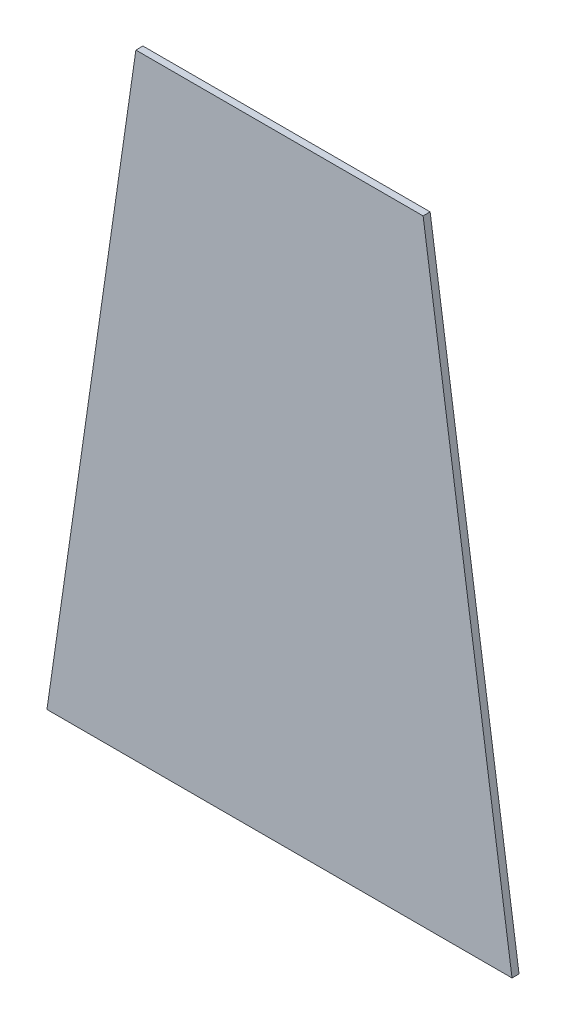
SolidWorks part; units mm, degrees
ref_plane "Front Plane" through (0, 0, 0) normal (0, 0, 1) x (1, 0, 0)
ref_plane "Top Plane" through (0, 0, 0) normal (0, 1, 0) x (1, 0, 0)
ref_plane "Right Plane" through (0, 0, 0) normal (1, 0, 0) x (0, 0, -1)
sketch "Sketch1" plane through (0, 0, 0) normal (0, 0, 1) x (1, 0, 0)
  line L0 (-66.675, 142.875) -> (-107.95, -142.875)
  line L1 (66.675, 142.875) -> (-66.675, 142.875)
  line L2 (66.675, 142.875) -> (66.675, -142.875)
  line L3 (66.675, -142.875) -> (-66.675, -142.875)
  line L4 (-66.675, 142.875) -> (-66.675, -142.875)
  line L5 (66.675, 142.875) -> (-66.675, -142.875) construction
  line L6 (66.675, -142.875) -> (-66.675, 142.875) construction
  line L7 (-107.95, -142.875) -> (-66.675, -142.875)
  line L8 (66.675, -142.875) -> (107.95, -142.875)
  line L9 (107.95, -142.875) -> (66.675, 142.875)
  point P0 (0, 0)
  dimension "D1" = 133.35
  dimension "D2" = 215.9
  dimension "D3" = 285.75
extrude "Boss-Extrude1" add sketch "Sketch1" along normal blind 3.2639 contours L0 L7 L4 | L1 L4 L3 L2 | L8 L9 L2
